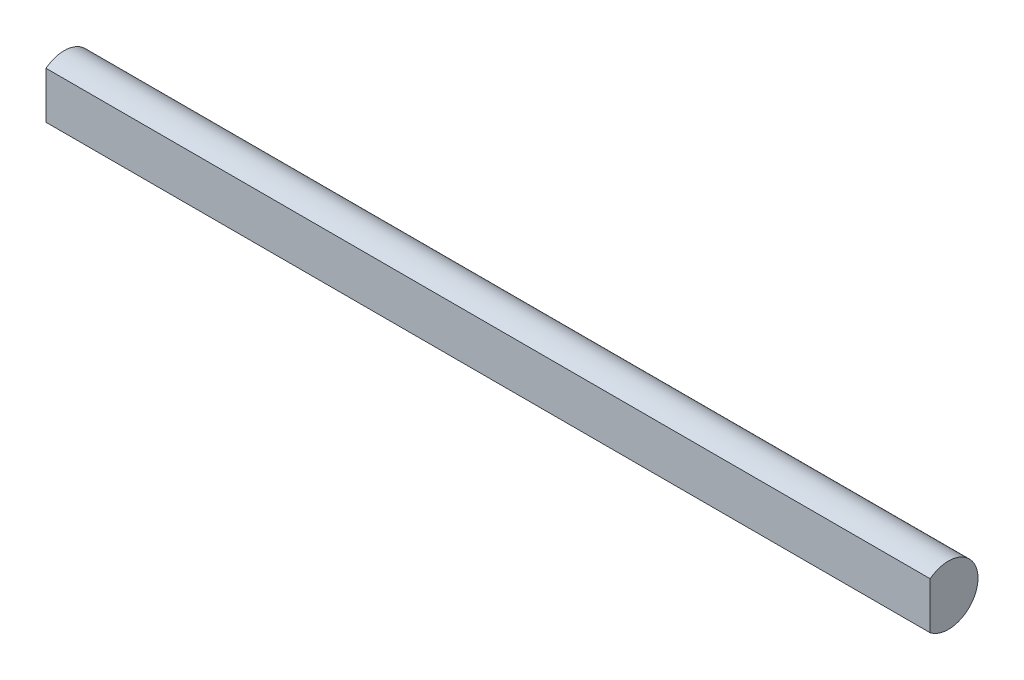
SolidWorks part; units mm, degrees
ref_plane "Front Plane" through (0, 0, 0) normal (0, 0, 1) x (1, 0, 0)
ref_plane "Top Plane" through (0, 0, 0) normal (0, 1, 0) x (1, 0, 0)
ref_plane "Right Plane" through (0, 0, 0) normal (1, 0, 0) x (0, 0, -1)
sketch "Sketch1" plane through (0, 0, 0) normal (1, 0, 0) x (0, 0, -1)
  line L0 (-1.7493, 2.25) -> (-1.7493, -2.25)
  arc A0 (-1.7493, -2.25) -> (-1.7493, 2.25) centre (0, 0) ccw
  dimension "D1" = 5.7
  dimension "D2" = 4.5
extrude "Boss-Extrude1" add sketch "Sketch1" along normal blind 85
